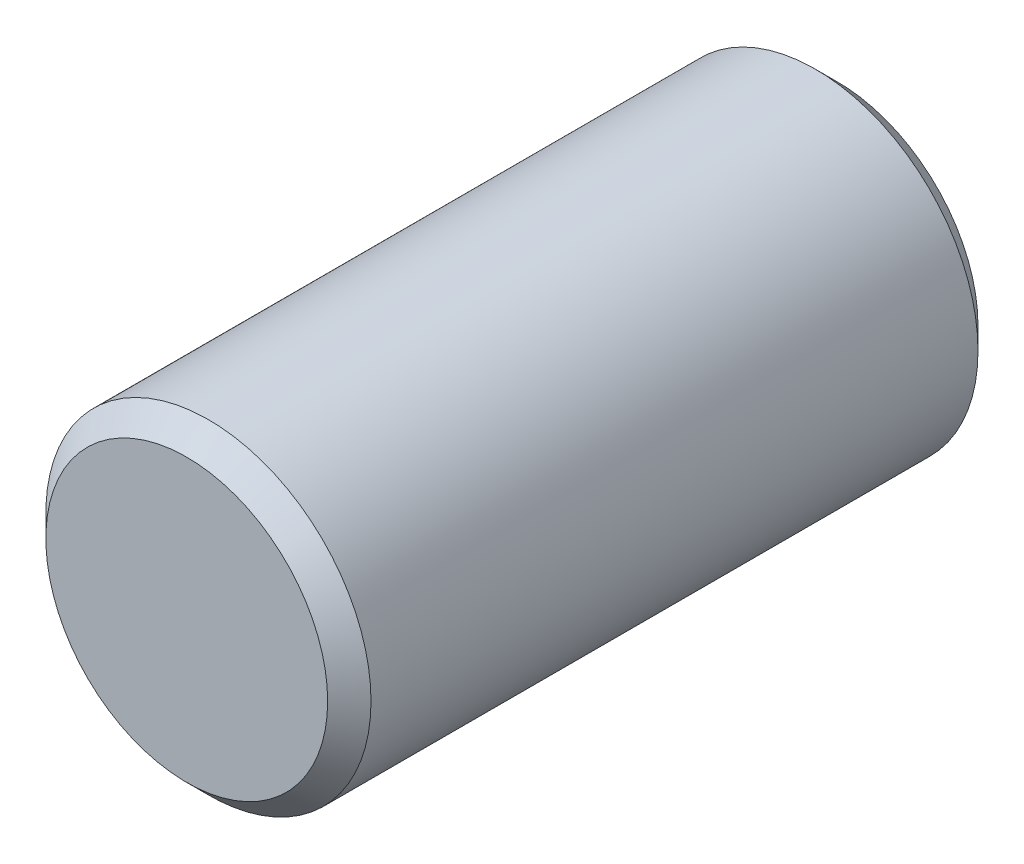
SolidWorks part; units mm, degrees
ref_plane "Front Plane" through (0, 0, 0) normal (0, 0, 1) x (1, 0, 0)
ref_plane "Top Plane" through (0, 0, 0) normal (0, 1, 0) x (1, 0, 0)
ref_plane "Right Plane" through (0, 0, 0) normal (1, 0, 0) x (0, 0, -1)
sketch "Sketch1" plane through (0, 0, 0) normal (0, 0, 1) x (1, 0, 0)
  circle A0 centre (0, 0) radius 0.375
  dimension "D1" = 0.75
extrude "Boss-Extrude1" add sketch "Sketch1" along normal mid plane 1.5
chamfer "Chamfer1" distance 0.05 angle 45 2 edges at (0.375, 0, -0.75) (0.375, 0, 0.75)
